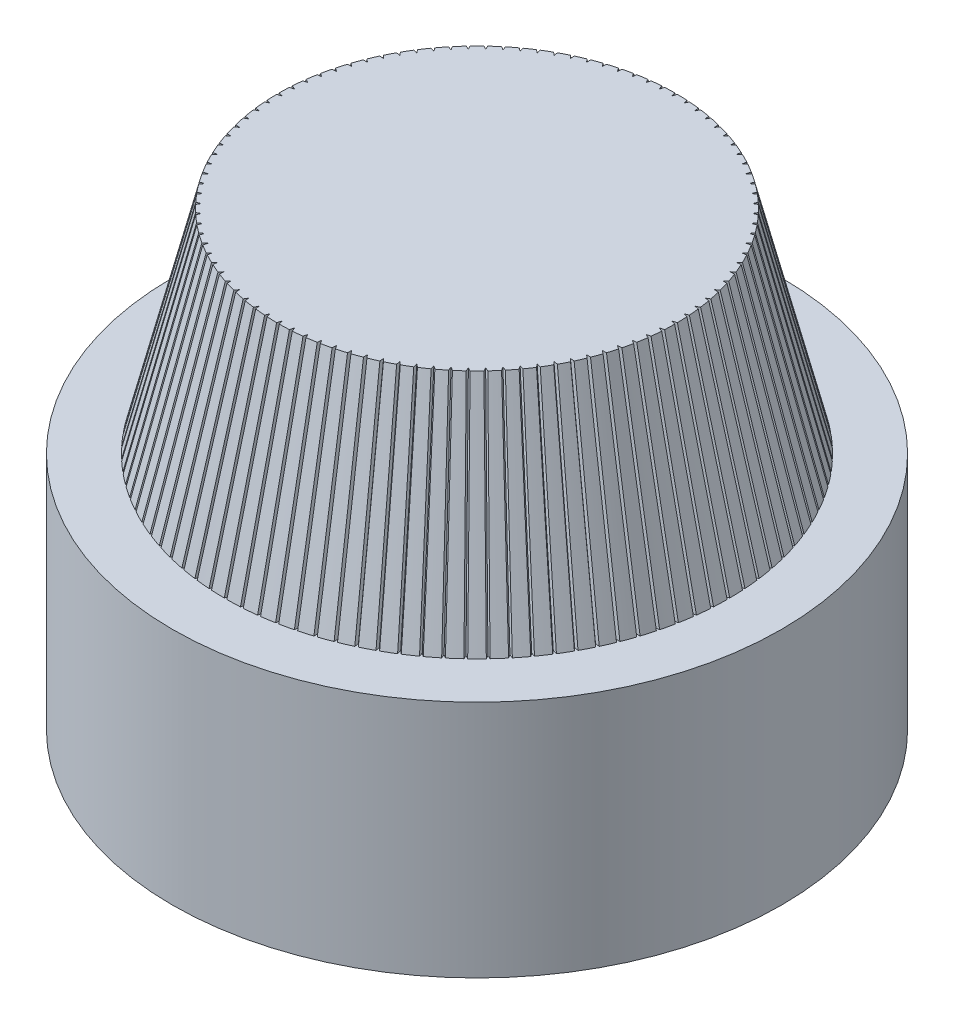
SolidWorks part; units mm, degrees
ref_plane "Alzado" through (0, 0, 0) normal (0, 0, 1) x (1, 0, 0)
ref_plane "Planta" through (0, 0, 0) normal (0, 1, 0) x (1, 0, 0)
ref_plane "Vista lateral" through (0, 0, 0) normal (1, 0, 0) x (0, 0, -1)
sketch "Croquis1" plane through (0, 0, 0) normal (0, 0, 1) x (1, 0, 0)
  line L0 (-16.0082, 0) -> (-14.0082, 0)
  line L1 (-16.0082, 0) -> (-16.0082, 9)
  line L2 (-16.0082, 9) -> (-14.0082, 9)
  line L3 (-14.0082, 9) -> (-12.0333, 9) construction
  line L4 (-12.0333, 9) -> (-12.0333, 17) construction
  line L5 (-14.0082, 9) -> (-12.0333, 17)
  line L6 (-12.0333, 17) -> (-4.5333, 17)
  line L7 (-14.0082, 0) -> (-14.0082, 4.5)
  line L8 (-14.0082, 4.5) -> (-4.5333, 4.5)
  line L9 (-4.5333, 4.5) -> (-4.5333, 17)
  dimension "D1" = 2
  dimension "D2" = 9
  dimension "D3" = 2
  dimension "D4" = 8
  dimension "D5" = 7.5
  dimension "D6" = 4.5
revolve "Revolución1" add sketch "Croquis1" angle 360 about L9
ref_plane "Plano1" through (0, 17, 0) normal (0, 1, 0) x (1, 0, 0)
ref_plane "Plano2" through (0, 9, 0) normal (0, 1, 0) x (1, 0, 0)
sketch "Croquis2" plane through (0, 17, 0) normal (0, 1, 0) x (1, 0, 0)
  line L0 (-4.5333, 7.5) -> (-4.5333, 1.3532) construction
  line L1 (-4.4824, 7.4998) -> (-4.5333, 7.3497)
  line L2 (-4.5843, 7.4998) -> (-4.5333, 7.3497)
  circle A0 centre (-4.5333, 0) radius 7.5 construction
  arc A1 (-4.5843, 7.4998) -> (-4.4824, 7.4998) centre (-4.5333, 0) cw
sketch "Croquis3" plane through (0, 9, 0) normal (0, 1, 0) x (1, 0, 0)
  line L0 (-4.5333, 11.4749) -> (-4.5333, 8.8608) construction
  line L5 (-4.4833, 9.4748) -> (-4.5333, 9.3228)
  line L6 (-4.5833, 9.4748) -> (-4.5333, 9.3228)
  circle A0 centre (-4.5333, 0) radius 11.4749 construction
  arc A1 (-4.5833, 9.4748) -> (-4.4833, 9.4748) centre (-4.5333, 9.0578) cw
  circle A3 centre (-4.5333, 0) radius 9.4749 construction
  dimension "D1" = 0.16
  dimension "D2" = 0.05
loft "Cortar-Recubrir1" cut profiles "Croquis3", "Croquis2"
pattern_circular "MatrizC1" count 100 over 360 about axis through (-4.5333, 17, 0) along (0, -1, 0) of "Cortar-Recubrir1"
sketch "Croquis4" plane through (0, 4.5, 0) normal (0, -1, 0) x (1, 0, 0)
  circle A0 centre (-4.5333, 0) radius 3
  circle A1 centre (-4.5333, 0) radius 9.4749 construction
  dimension "D1" = 6
extrude "Cortar-Extruir1" cut sketch "Croquis4" against normal blind 10
